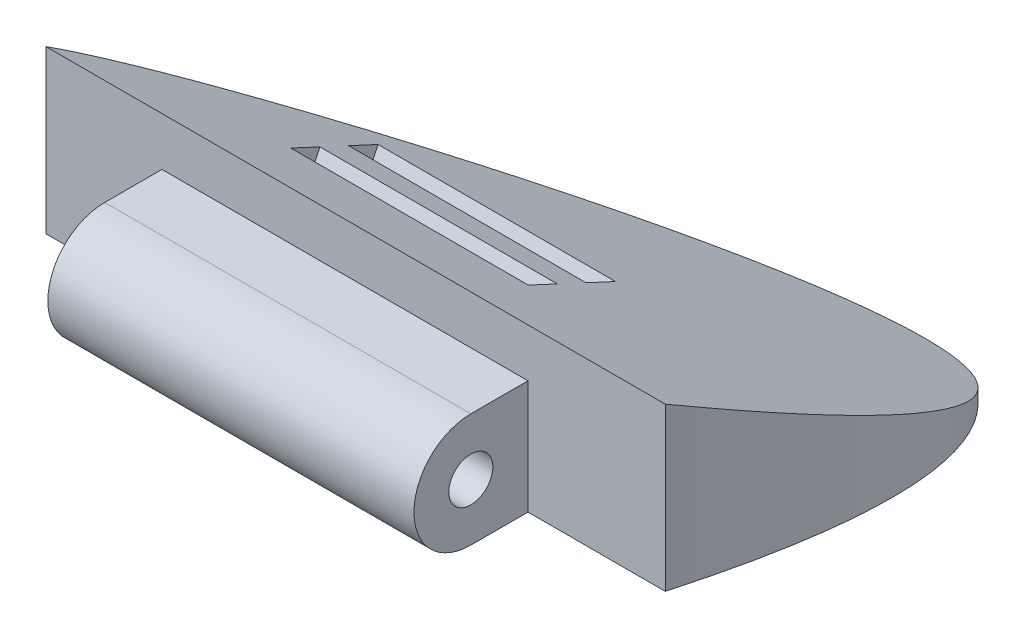
SolidWorks part; units mm, degrees
ref_plane "Front Plane" through (0, 0, 0) normal (0, 0, 1) x (1, 0, 0)
ref_plane "Top Plane" through (0, 0, 0) normal (0, 1, 0) x (1, 0, 0)
ref_plane "Right Plane" through (0, 0, 0) normal (1, 0, 0) x (0, 0, -1)
sketch "Sketch1" plane through (0, 0, 0) normal (0, 1, 0) x (1, 0, 0)
  line L0 (0, 0) -> (19.217, 0)
  line L1 (19.217, 0) -> (19.217, 6.0053)
  line L2 (19.217, 6.0053) -> (26.4233, 6.0053)
  line L3 (0, 0) -> (0, 6.0053)
  line L4 (0, 6.0053) -> (-6.0854, 6.0053)
  spline S0 degree 3 poles (26.4233, 6.0053) (36.5595, 42.6631) (-2.021, 14.397) (-6.0854, 6.0053) knots 0 0 0 0 1 1 1 1
extrude "Boss-Extrude1" add sketch "Sketch1" along normal blind 12.7
sketch "Sketch2" plane through (0, 12.7, 0) normal (0, 1, 0) x (1, 0, 0)
  line L1 (0, 6.0053) -> (19.217, 6.0053)
  line L2 (0, 6.0053) -> (0, 0)
  line L3 (0, 0) -> (19.217, 0)
  line L4 (19.217, 6.0053) -> (19.217, 0)
extrude "Cut-Extrude1" cut sketch "Sketch2" against normal blind 2.54
sketch "Sketch3" plane through (19.217, 0, 0) normal (1, 0, 0) x (0, 0, -1)
  line L0 (6.0053, 12.7) -> (6.0053, 0) construction
  line L1 (0, 10.16) -> (6.0053, 10.16)
  line L2 (0, 10.16) -> (0, 4.1896)
  line L3 (0, 4.1896) -> (6.0053, 4.1896)
  line L4 (6.0053, 10.16) -> (6.0053, 4.1896)
  line L5 (6.0053, 4.1896) -> (24.3276, 4.1896)
  line L6 (24.3276, 0) -> (24.3276, 12.7) construction
  line L7 (24.3276, 4.1896) -> (6.0053, 12.7)
  line L8 (6.0053, 12.7) -> (6.0053, 10.16)
  line L9 (6.0053, 12.7) -> (24.3276, 12.7)
  line L10 (24.3276, 12.7) -> (6.0053, 12.7) construction
  line L11 (24.3276, 12.7) -> (24.3276, 0)
  line L12 (24.3276, 0) -> (0, 0)
  line L13 (0, 0) -> (0, 4.1896)
  line L14 (6.0053, 10.16) -> (6.0053, 12.7)
  arc A0 (3.0026, 10.16) -> (3.0026, 4.1896) centre (3.0026, 7.1748) ccw
  circle A1 centre (3.0026, 7.1748) radius 1.1552
  line M8 (0, 10.16) -> (0, 0)
  line M9 (0, 0) -> (6.0053, 0)
  line M10 (6.0053, 0) -> (6.0053, 10.16)
extrude "Cut-Extrude2" cut sketch "Sketch3" against normal blind 26.924 and the other way blind 11.684 contours L11 L9 L7 | L12 L11 L5 M10 | L3 M8 M9 M10 | A0 L1 L3 M8 | A1
sketch "Sketch4" plane through (0, 12.7406, -5.9178) normal (0, 0.9069, -0.4213) x (1, 0, 0)
  line L0 (9.6085, -3.2844) -> (9.6085, 15.6114) construction
  line L2 (3.3779, 3.8349) -> (15.839, 3.8349)
  line L3 (15.839, 3.8349) -> (15.839, 8.8819)
  line L4 (15.839, 8.8819) -> (3.3779, 8.8819)
  line L5 (9.6085, 8.8819) -> (9.6085, 7.1756)
  line L6 (3.3779, 7.1756) -> (15.839, 7.1756)
  line L7 (9.6085, 3.8349) -> (9.6085, 5.5172)
  line L8 (3.3779, 5.5172) -> (15.839, 5.5172)
  line L9 (3.3779, 3.8349) -> (3.3779, 8.8819)
extrude "Cut-Extrude4" cut sketch "Sketch4" against normal blind 3.81 contours L9 L6 L5 L4 | L5 L6 L3 L4 | L8 L7 L2 L3 | L9 L2 L7 L8
sketch "Sketch5" plane through (0, -2.3242, -5.0038) normal (0, 0.4213, 0.9069) x (1, 0, 0)
  line L1 (15.839, 14.0479) -> (2.7174, 14.0479)
  line L2 (15.839, 14.0479) -> (15.839, 10.1948)
  line L3 (15.839, 10.1948) -> (2.7174, 10.1948)
  line L4 (2.7174, 14.0479) -> (2.7174, 10.1948)
  line L5 (2.7174, 10.1948) -> (15.839, 10.1948)
  line L6 (2.7174, 10.1948) -> (2.7174, 12.1213)
  line L7 (2.7174, 12.1213) -> (15.839, 12.1213)
  line L8 (15.839, 10.1948) -> (15.839, 12.1213)
  line M2 (3.3779, 14.0479) -> (3.3779, 10.2379)
  line M3 (3.3779, 10.2379) -> (15.839, 10.2379)
  line M4 (15.839, 10.2379) -> (15.839, 14.0479)
extrude "Cut-Extrude5" cut sketch "Sketch5" against normal blind 2.54 contours L7 M2 M3 M4
sketch "Sketch6" plane through (0, 4.1896, 0) normal (0, -1, 0) x (-1, 0, 0)
  line L0 (-9.6085, 0.0174) -> (-9.6085, 21.6986) construction
  line L2 (-9.6085, 8.3869) -> (-9.6085, 10.0736)
  line L3 (-3.171, 8.3869) -> (-16.046, 8.3869)
  line L4 (-9.6085, 8.3869) -> (-9.6085, 13.5102)
  line L5 (-3.171, 13.5102) -> (-16.046, 13.5102)
  line L6 (-16.046, 8.3869) -> (-16.046, 13.5102)
  line L7 (-3.171, 10.0736) -> (-16.046, 10.0736)
  line L8 (-9.6085, 13.5102) -> (-9.6085, 11.8529)
  line L9 (-3.171, 11.8529) -> (-16.046, 11.8529)
  line L10 (-3.171, 8.3869) -> (-3.171, 13.5102)
extrude "Cut-Extrude6" cut sketch "Sketch6" against normal blind 3.81 and the other way through all contours L3 L10 L7 L2 | L2 L7 L6 L3 | L9 L4 L5 L6 | L9 L10 L5 L4
equation "\"0.15n\"=0.1"
